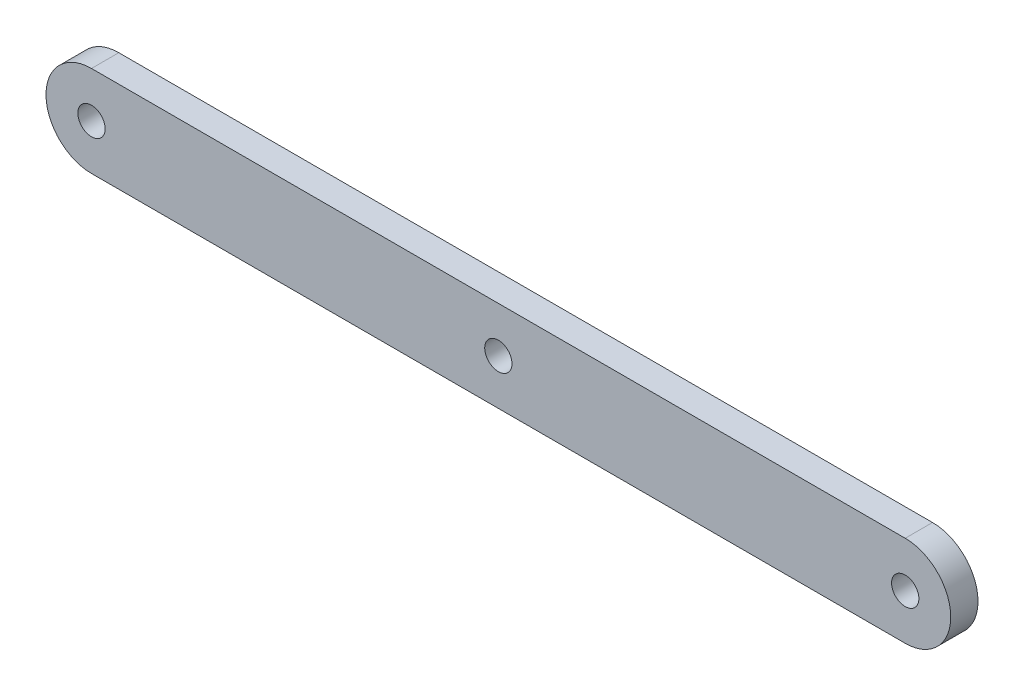
SolidWorks part; units mm, degrees
ref_plane "前基準面" through (0, 0, 0) normal (0, 0, 1) x (1, 0, 0)
ref_plane "上基準面" through (0, 0, 0) normal (0, 1, 0) x (1, 0, 0)
ref_plane "右基準面" through (0, 0, 0) normal (1, 0, 0) x (0, 0, -1)
sketch "草圖1" plane through (0, 0, 0) normal (0, 0, 1) x (1, 0, 0)
  line L0 (-22.36, 0) -> (22.36, 0) construction
  line L1 (-22.36, 2.5) -> (22.36, 2.5)
  line L2 (-22.36, -2.5) -> (22.36, -2.5)
  arc A0 (-22.36, 2.5) -> (-22.36, -2.5) centre (-22.36, 0) ccw
  arc A1 (22.36, -2.5) -> (22.36, 2.5) centre (22.36, 0) ccw
  circle A2 centre (22.36, 0) radius 0.75
  circle A3 centre (-22.36, 0) radius 0.75
  circle A4 centre (0, 0) radius 0.75
  point P2 (0, 0)
  point P9 (0, 0)
  point P15 (0, 0)
  point P16 (-22.36, 0)
  dimension "D2" = 2.5
  dimension "D3" = 1.5
  dimension "D1" = 44.72
extrude "填料-伸長1" add sketch "草圖1" along normal mid plane 1.5
